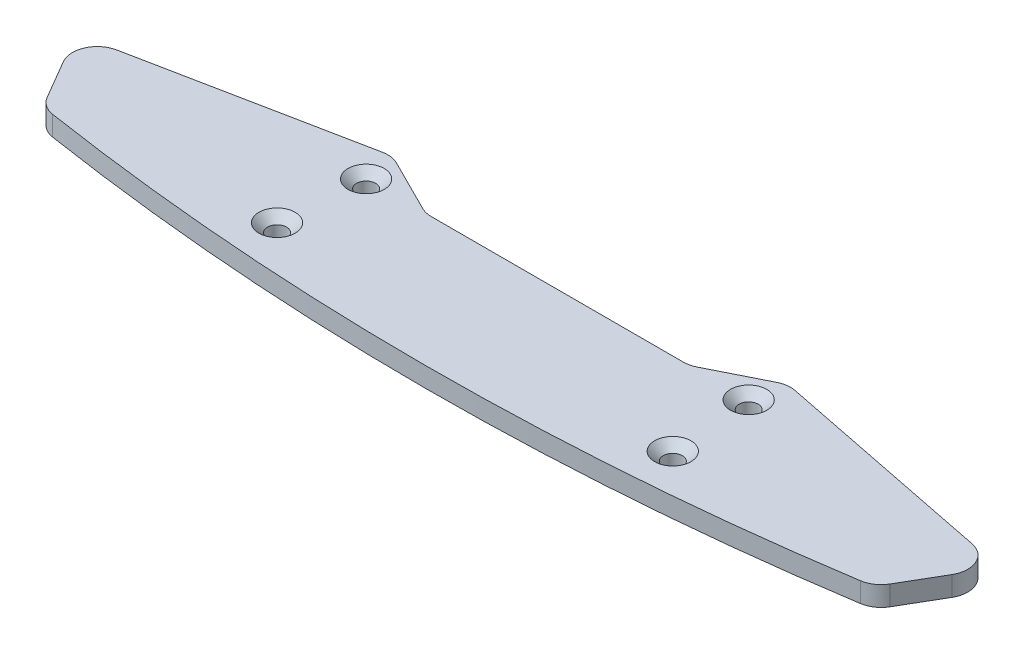
SolidWorks part; units mm, degrees
material "Delrin 2700 NC010, Low Viscosity Acetal Copolymer (SS)"
ref_plane "Front Plane" through (0, 0, 0) normal (0, 0, 1) x (1, 0, 0)
ref_plane "Top Plane" through (0, 0, 0) normal (0, 1, 0) x (1, 0, 0)
ref_plane "Right Plane" through (0, 0, 0) normal (1, 0, 0) x (0, 0, -1)
sketch "Sketch1" plane through (0, 0, 0) normal (0, 1, 0) x (1, 0, 0)
  line L0 (0, 0) -> (0, -20)
  line L1 (0, 0) -> (20, 0)
  line L2 (20, 0) -> (30, 5)
  line L3 (30, 5) -> (70, -3)
  line L4 (70, -3) -> (63, -15)
  line L5 (0, -20) -> (-10.1494, -20) construction
  arc A0 (0, -20) -> (63, -15) centre (0, 379.4) ccw
  dimension "D1" = 70
  dimension "D2" = 20
  dimension "D3" = 25
  dimension "D4" = 3
  dimension "D5" = 5
  dimension "D6" = 40
  dimension "D7" = 12
  dimension "D8" = 7
extrude "Boss-Extrude1" add sketch "Sketch1" along normal blind 3
hole_wizard "CSK for M2.5 Flat Head Machine Screw1" positions "Sketch4" profile "Sketch3" countersink size "M2.5" standard "ANSI Metric" end condition through all
sketch "Sketch4" plane through (0, 3, 0) normal (0, 1, 0) x (1, 0, 0)
  line L0 (0, 0) -> (0, -20) construction
  line L1 (20, 0) -> (0, 0) construction
  point P0 (29, 0)
  point P2 (30, -12.5)
  dimension "D1" = 29
  dimension "D2" = 30
  dimension "D3" = 12.5
sketch "Sketch3" plane through (29, 3, 0) normal (1, 0, 0) x (0, 0, 1)
  line L0 (0, 0) -> (0, 3)
  line L1 (0, 3) -> (1.45, 3)
  line L2 (1.45, 3) -> (1.45, 1.3)
  line L3 (1.45, 1.3) -> (2.75, 0)
  line L5 (2.75, 0) -> (0, 0)
  line L6 (-1.45, 1.3) -> (-2.75, 0) construction
  line L11 (0, -6.35) -> (0, 107.95) construction
  dimension "Thru Hole Dia." = 2.9
  dimension "Thru Hole Depth" = 3
  dimension "Near C'Sink Dia." = 5.5
  dimension "Near C'Sink Angle" = 90
mirror "Mirror1" about plane through (0, 0, 0) normal (1, 0, 0) of "CSK for M2.5 Flat Head Machine Screw1", "Boss-Extrude1"
fillet "Fillet1" radius 3.75 8 edges at (20, 1.5, 0) (30, 1.5, -5) (70, 1.5, 3) (63, 1.5, 15) (-70, 1.5, 3) (-30, 1.5, -5) (-20, 1.5, 0) (-63, 1.5, 15)
